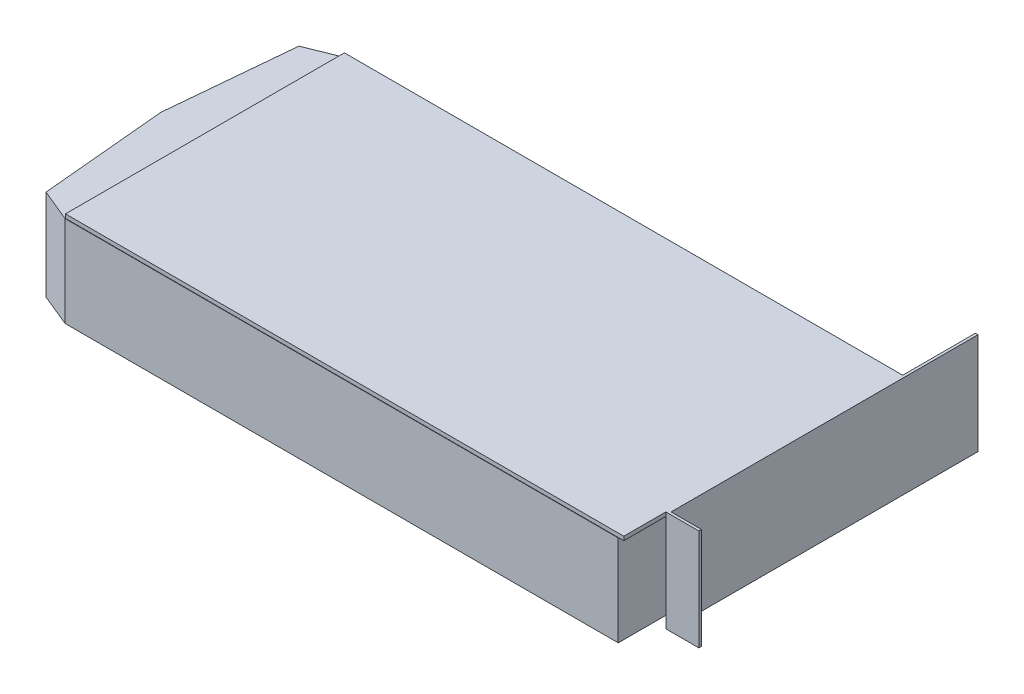
SolidWorks part; units mm, degrees
ref_plane "Front Plane" through (0, 0, 0) normal (0, 0, 1) x (1, 0, 0)
ref_plane "Top Plane" through (0, 0, 0) normal (0, 1, 0) x (1, 0, 0)
ref_plane "Right Plane" through (0, 0, 0) normal (1, 0, 0) x (0, 0, -1)
sketch "card" plane through (0, 0, 0) normal (0, 1, 0) x (1, 0, 0)
  line L0 (0, 0) -> (0, 107.4)
  line L1 (0, 107.4) -> (215, 107.4)
  line L2 (0, 0) -> (215, 0)
  line L3 (215, 0) -> (215, 107.4)
  dimension "D1" = 215
  dimension "D2" = 107.4
extrude "Boss-Extrude1" add sketch "card" along normal blind 1.5
sketch "Sketch2" plane through (215, 0, 0) normal (1, 0, 0) x (0, 0, -1)
  line L0 (0, 1.5) -> (16.2, 1.5) construction
  line L1 (0, 1.5) -> (107.4, 1.5) construction
  line L2 (16.2, 1.5) -> (16.2, -37.5)
  line L3 (16.2, 1.5) -> (135.4, 1.5)
  line L4 (16.2, -37.5) -> (135.4, -37.5)
  line L5 (135.4, -37.5) -> (135.4, 1.5)
  line L6 (0, 0) -> (107.4, 0) construction
  dimension "D1" = 28
  dimension "D2" = 91.2
  dimension "D3" = 37.5
extrude "Boss-Extrude2" add sketch "Sketch2" along normal blind 1
sketch "Sketch3" plane through (216, 0, 0) normal (1, 0, 0) x (0, 0, -1)
  line L0 (16.2, 1.5) -> (17.2, 1.5)
  line L1 (135.4, 1.5) -> (16.2, 1.5) construction
  line L2 (17.2, 1.5) -> (17.2, -37.5)
  line L3 (16.2, -37.5) -> (135.4, -37.5) construction
  line L4 (17.2, -37.5) -> (16.2, -37.5)
  line L5 (16.2, -37.5) -> (16.2, 1.5)
  dimension "D1" = 1
extrude "Boss-Extrude3" add sketch "Sketch3" along normal blind 11.7
sketch "Sketch5" plane through (0, 0, 0) normal (0, -1, 0) x (1, 0, 0)
  line L1 (215, 0) -> (213, 0) construction
  line L2 (0, 0) -> (215, 0) construction
  line L6 (213, 0) -> (213, -107.4)
  line L7 (215, -107.4) -> (0, -107.4) construction
  line L8 (0, -107.4) -> (-12.5, -102.4)
  line L9 (213, -107.4) -> (0, -107.4)
  line L10 (0, -107.4) -> (0, 0) construction
  line L11 (-17, -53.7) -> (-12.5, -102.4)
  line L12 (-17, -53.7) -> (-12.5, -5)
  line L13 (-12.5, -5) -> (0, 0.1411)
  line L14 (0, 0.1411) -> (213, 0.1411)
  line L15 (213, 0.1411) -> (213, 0)
  dimension "D1" = 213
extrude "Boss-Extrude4" add sketch "Sketch5" along normal blind 35
